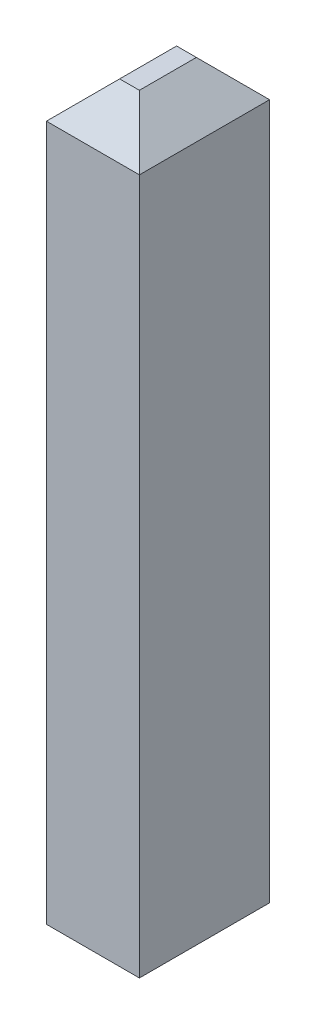
SolidWorks part; units mm, degrees
ref_plane "Front Plane" through (0, 0, 0) normal (0, 0, 1) x (1, 0, 0)
ref_plane "Top Plane" through (0, 0, 0) normal (0, 1, 0) x (1, 0, 0)
ref_plane "Right Plane" through (0, 0, 0) normal (1, 0, 0) x (0, 0, -1)
sketch "Sketch1" plane through (0, 0, 0) normal (0, 1, 0) x (1, 0, 0)
  line L1 (-0.127, -0.1778) -> (0.127, -0.1778)
  line L2 (-0.127, -0.1778) -> (-0.127, 0.1778)
  line L3 (-0.127, 0.1778) -> (0.127, 0.1778)
  line L4 (0.127, -0.1778) -> (0.127, 0.1778)
  line L5 (-0.127, -0.1778) -> (0.127, 0.1778) construction
  line L6 (-0.127, 0.1778) -> (0.127, -0.1778) construction
  point P0 (0, 0)
  dimension "D1" = 0.254
  dimension "D2" = 0.3556
extrude "Boss-Extrude1" add sketch "Sketch1" along normal blind 2
chamfer "Chamfer1" distance 0.1 angle 45 2 edges at (0, 2, -0.1778) (0, 2, 0.1778)
chamfer "Chamfer2" distance 0.1 angle 45 2 edges at (-0.127, 2, 0) (0.127, 2, 0)
